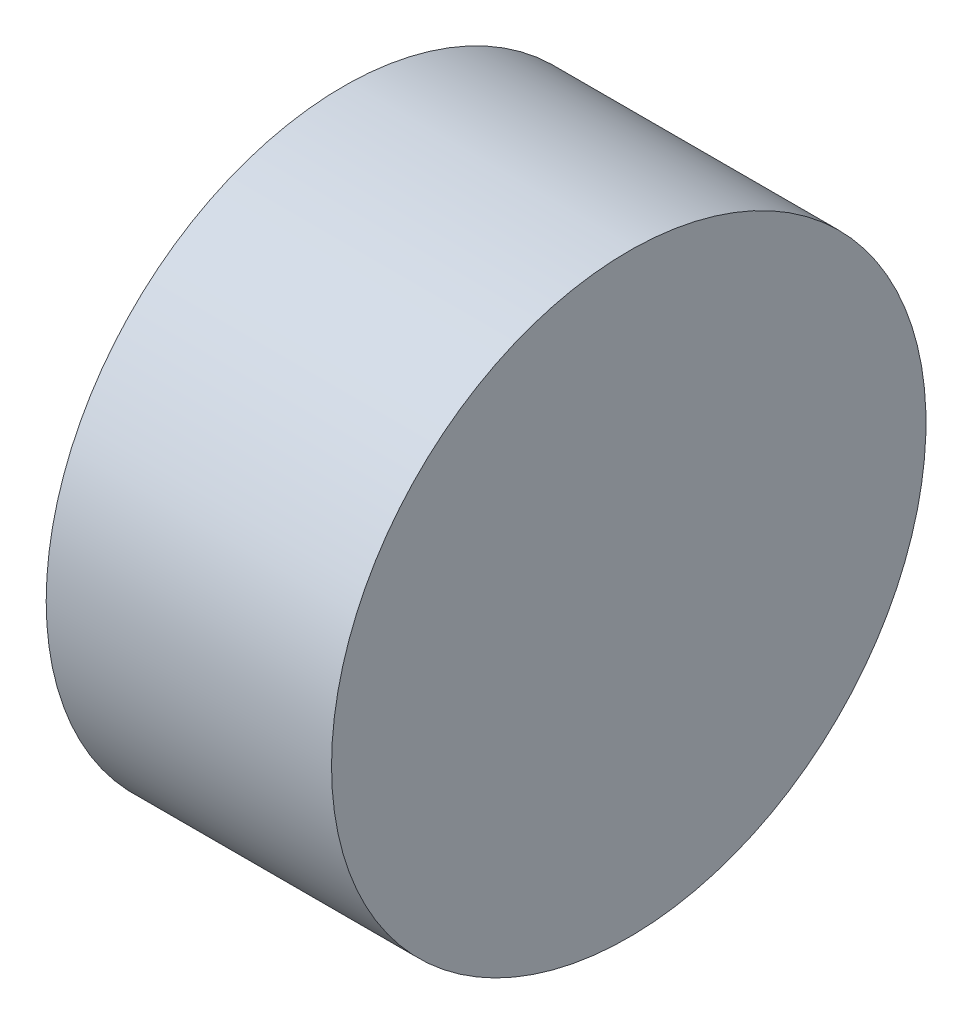
SolidWorks part; units mm, degrees
ref_plane "前视基准面" through (0, 0, 0) normal (0, 0, 1) x (1, 0, 0)
ref_plane "上视基准面" through (0, 0, 0) normal (0, 1, 0) x (1, 0, 0)
ref_plane "右视基准面" through (0, 0, 0) normal (1, 0, 0) x (0, 0, -1)
sketch "草图1" plane through (0, 0, 0) normal (0, 0, 1) x (1, 0, 0)
  line L0 (127.0004, 38.6466) -> (140.107, 38.6466) construction
  line L1 (130.0786, 38.6466) -> (130.0786, 44.8966)
  line L2 (136.0786, 38.6466) -> (136.0786, 44.8966)
  line L3 (130.0786, 38.6466) -> (136.0786, 38.6466)
  line L5 (130.0786, 44.8966) -> (136.0786, 44.8966)
  dimension "D1" = 6
revolve "旋转1" add sketch "草图1" angle 360 about L0
